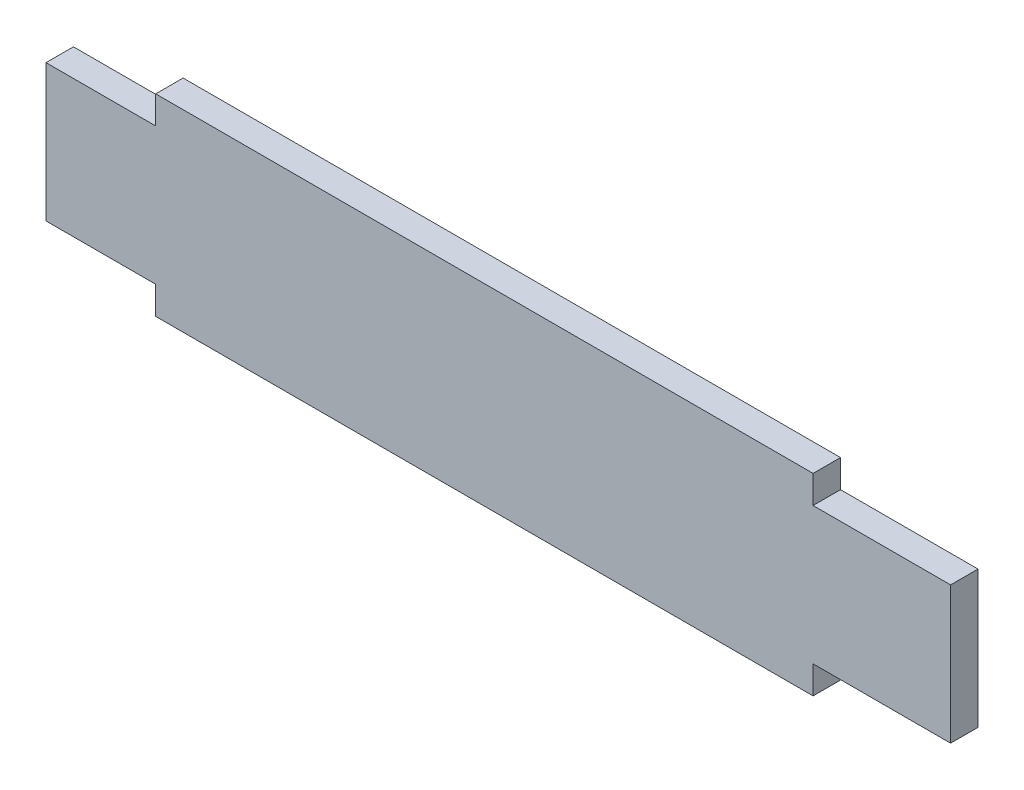
SolidWorks part; units mm, degrees
ref_plane "正面" through (0, 0, 0) normal (0, 0, 1) x (1, 0, 0)
ref_plane "平面" through (0, 0, 0) normal (0, 1, 0) x (1, 0, 0)
ref_plane "右側面" through (0, 0, 0) normal (1, 0, 0) x (0, 0, -1)
sketch "ｽｹｯﾁ1" plane through (0, 0, 0) normal (0, 0, 1) x (1, 0, 0)
  line L0 (164.93, 12.5) -> (177.1233, 12.5) construction
  line L1 (0, 0) -> (164.93, 0)
  line L2 (0, 0) -> (0, 25)
  line L3 (0, 25) -> (164.93, 25)
  line L4 (164.93, 0) -> (164.93, 25)
  line L5 (139.86, 25) -> (20, 25)
  line L6 (139.86, 25) -> (139.86, 30.07)
  line L7 (139.86, 30.07) -> (20, 30.07)
  line L8 (20, 25) -> (20, 30.07)
  line L9 (139.86, -5.07) -> (20, -5.07)
  line L10 (20, 0) -> (20, -5.07)
  line L11 (139.86, 0) -> (20, 0)
  line L12 (139.86, 0) -> (139.86, -5.07)
  line L13 (79.93, -5.07) -> (79.93, 14.4644) construction
  point P9 (20, 27.535)
  dimension "D1" = 164.93
  dimension "D2" = 25
  dimension "D3" = 5.07
  dimension "D4" = 25.07
  dimension "D5" = 20
extrude "ﾎﾞｽ - 押し出し1" add sketch "ｽｹｯﾁ1" along normal blind 5
